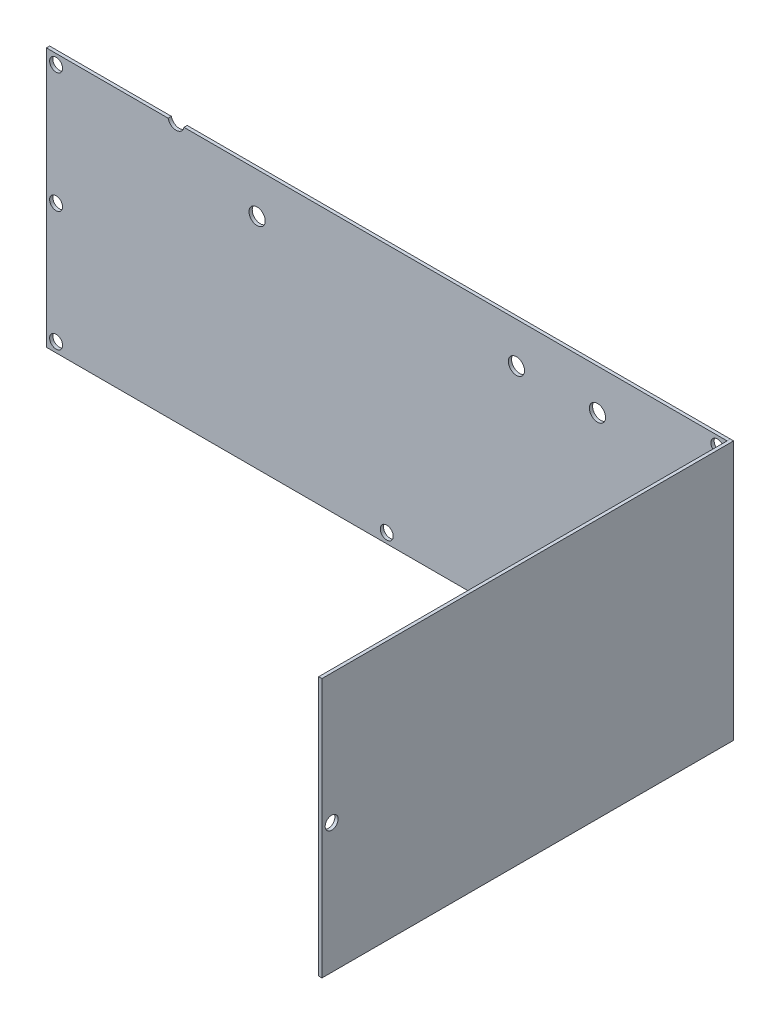
SolidWorks part; units mm, degrees
ref_plane "前视" through (0, 0, 0) normal (0, 0, 1) x (1, 0, 0)
ref_plane "上视" through (0, 0, 0) normal (0, 1, 0) x (1, 0, 0)
ref_plane "右视" through (0, 0, 0) normal (1, 0, 0) x (0, 0, -1)
sketch "草图1" plane through (0, 0, 0) normal (0, 0, 1) x (1, 0, 0)
  line L0 (-105, -40) -> (105, -40)
  line L1 (-105, -40) -> (-105, 40)
  line L2 (105, -40) -> (105, 40)
  line L3 (-105, 40) -> (105, 40)
  line L4 (-105, -40) -> (105, 40) construction
  line L5 (105, -40) -> (-105, 40) construction
  point P2 (0, 0)
  dimension "D1" = 80
  dimension "D2" = 210
extrude "凸台-拉伸1" add sketch "草图1" along normal blind 1
sketch "草图2" plane through (0, 0, 1) normal (0, 0, 1) x (1, 0, 0)
  line L1 (105, 40) -> (106, 40)
  line L2 (105, 40) -> (105, -40)
  line L3 (105, -40) -> (106, -40)
  line L4 (106, 40) -> (106, -40)
  dimension "D1" = 80
  dimension "D2" = 1
extrude "凸台-拉伸2" add sketch "草图2" along normal blind 126 and the other way blind 1 separate body
sketch "草图3" plane through (0, 0, 0) normal (0, 0, -1) x (-1, 0, 0)
  line L0 (105, 40) -> (105, -40) construction
  line L1 (-105, 40) -> (105, 40) construction
  line L2 (-105, 40) -> (-105, -40) construction
  line L3 (105, -40) -> (-105, -40) construction
  line L4 (105, -40) -> (-105, -40) construction
  circle A0 centre (102, 0) radius 2
  circle A1 centre (102, 37) radius 2
  circle A2 centre (102, -37) radius 2
  circle A4 centre (-102, 37) radius 2
  circle A5 centre (0, -37) radius 2
  circle A6 centre (-102, -37) radius 2
  point P6 (0, -40)
  dimension "D1" = 3
  dimension "D5" = 3
  dimension "D2" = 40
  dimension "D6" = 37
  dimension "D7" = 37
  dimension "D8" = 3
  dimension "D9" = 3
  dimension "D10" = 102
  dimension "D11" = 102
  dimension "D12" = 3
  dimension "D3" = 2
  dimension "D4" = 2
extrude "切除-拉伸1" cut sketch "草图3" against normal blind 2
sketch "草图5" plane through (106, 0, 0) normal (1, 0, 0) x (0, 0, -1)
  circle A0 centre (-124, 50) radius 2
  circle A5 centre (-64, -50) radius 2
  circle A6 centre (-4, -50) radius 2
  circle A7 centre (-124, 0) radius 2
extrude "切除-拉伸2" cut sketch "草图5" against normal blind 2
sketch "草图6" plane through (0, 0, 0) normal (0, 0, -1) x (-1, 0, 0)
  line L0 (-65, 27.5) -> (-40, 27.5) construction
  line L1 (-105, 40) -> (105, 40) construction
  line L2 (-105, -40) -> (-105, 40) construction
  line L3 (-40, 27.5) -> (40, 27.5) construction
  line L4 (65, 40.5) -> (40, 27.5) construction
  circle A0 centre (-65, 27.5) radius 2.5
  circle A1 centre (-40, 27.5) radius 2.5
  circle A2 centre (40, 27.5) radius 2.5
  circle A3 centre (65, 40.5) radius 2.5
  dimension "D1" = 25
  dimension "D2" = 12.5
  dimension "D3" = 40
extrude "切除-拉伸3" cut sketch "草图6" against normal blind 2
